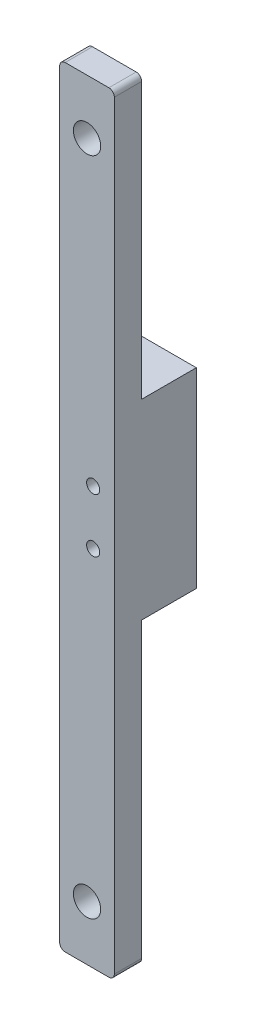
SolidWorks part; units mm, degrees
ref_plane "Front Plane" through (0, 0, 0) normal (0, 0, 1) x (1, 0, 0)
ref_plane "Top Plane" through (0, 0, 0) normal (0, 1, 0) x (1, 0, 0)
ref_plane "Right Plane" through (0, 0, 0) normal (1, 0, 0) x (0, 0, -1)
sketch "Sketch1" plane through (0, 0, 0) normal (0, 0, 1) x (1, 0, 0)
  line L1 (0, 0) -> (10, 0)
  line L2 (0, 0) -> (0, 141)
  line L3 (0, 141) -> (10, 141)
  line L4 (10, 0) -> (10, 141)
  circle A0 centre (5, 131) radius 2.5
  circle A1 centre (5, 10) radius 2.5
extrude "Boss-Extrude1" add sketch "Sketch1" along normal blind 5
sketch "Sketch3" plane through (0, 0, 0) normal (0, 0, -1) x (-1, 0, 0)
  line L0 (0, 141) -> (0, 0) construction
  line L1 (0, 89.6211) -> (-10, 89.6211)
  line L2 (0, 89.6211) -> (0, 54.6211)
  line L3 (0, 54.6211) -> (-10, 54.6211)
  line L4 (-10, 89.6211) -> (-10, 54.6211)
  line L5 (-10, 0) -> (-10, 141) construction
extrude "Boss-Extrude3" add sketch "Sketch3" along normal blind 10
sketch "Sketch4" plane through (0, 0, -10) normal (0, 0, -1) x (-1, 0, 0)
  circle A0 centre (-6.1182, 66.494) radius 1.2
  circle A1 centre (-6.1182, 76.394) radius 1.2
extrude "Cut-Extrude1" cut sketch "Sketch4" against normal blind 15
fillet "Fillet1" radius 1 4 edges at (0, 0, 2.5) (10, 0, 2.5) (0, 141, 2.5) (10, 141, 2.5)
